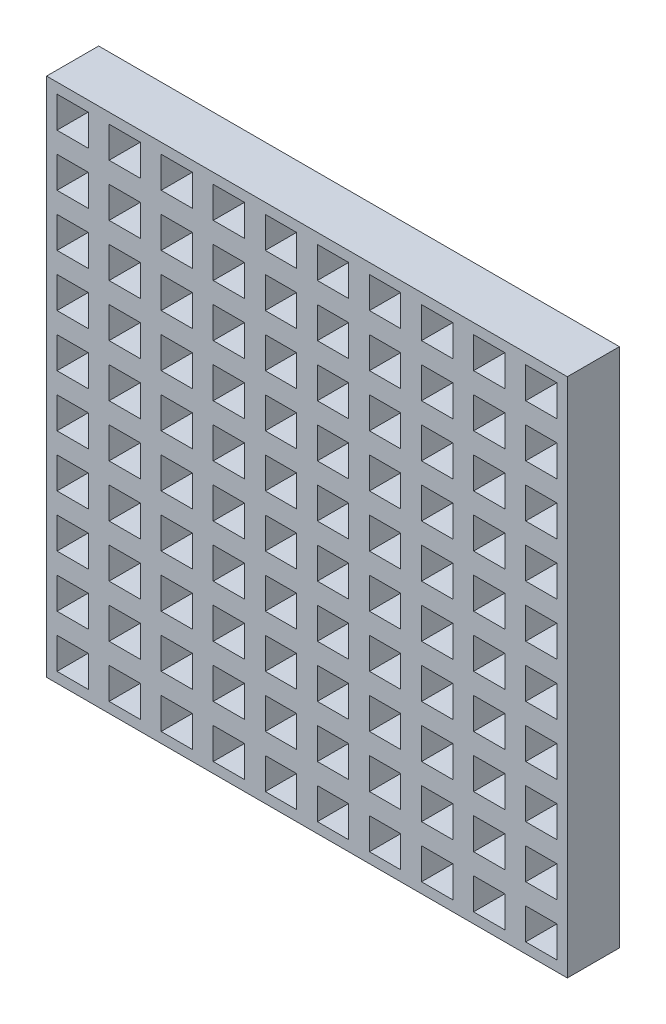
SolidWorks part; units mm, degrees
material "201.0-T7 Insulated Mold Casting (SS)"
ref_plane "Front Plane" through (0, 0, 0) normal (0, 0, 1) x (1, 0, 0)
ref_plane "Top Plane" through (0, 0, 0) normal (0, 1, 0) x (1, 0, 0)
ref_plane "Right Plane" through (0, 0, 0) normal (1, 0, 0) x (0, 0, -1)
sketch "Sketch1" plane through (0, 0, 0) normal (0, 0, 1) x (1, 0, 0)
  line L1 (-12.7, -12.7) -> (12.7, -12.7)
  line L2 (-12.7, -12.7) -> (-12.7, 12.7)
  line L3 (-12.7, 12.7) -> (12.7, 12.7)
  line L4 (12.7, -12.7) -> (12.7, 12.7)
  line L5 (-12.7, -12.7) -> (12.7, 12.7) construction
  line L6 (-12.7, 12.7) -> (12.7, -12.7) construction
  point P0 (0, 0)
  dimension "D1" = 25.4
  dimension "D2" = 25.4
extrude "Boss-Extrude1" add sketch "Sketch1" along normal blind 2.54
sketch "Sketch2" plane through (0, 0, 2.54) normal (0, 0, 1) x (1, 0, 0)
  line L0 (-12.7, 12.7) -> (-12.7, -12.7)
  line L1 (-10.16, 12.7) -> (-10.16, -12.7)
  line L2 (-7.62, 12.7) -> (-7.62, -12.7)
  line L3 (-5.08, 12.7) -> (-5.08, -12.7)
  line L4 (-2.54, 12.7) -> (-2.54, -12.7)
  line L5 (0, 12.7) -> (0, -12.7)
  line L6 (2.54, 12.7) -> (2.54, -12.7)
  line L7 (5.08, 12.7) -> (5.08, -12.7)
  line L8 (7.62, 12.7) -> (7.62, -12.7)
  line L9 (10.16, 12.7) -> (10.16, -12.7)
  line L10 (-12.7, 12.7) -> (12.7, 12.7)
  line L11 (-12.7, 10.16) -> (12.7, 10.16)
  line L12 (12.7, -12.7) -> (12.7, 12.7) construction
  line L13 (-12.7, 7.62) -> (12.7, 7.62)
  line L14 (-12.7, 5.08) -> (12.7, 5.08)
  line L15 (-12.7, 2.54) -> (12.7, 2.54)
  line L16 (-12.7, 0) -> (12.7, 0)
  line L17 (-12.7, -2.54) -> (12.7, -2.54)
  line L18 (-12.7, -5.08) -> (12.7, -5.08)
  line L19 (-12.7, -7.62) -> (12.7, -7.62)
  line L20 (-12.7, -10.16) -> (12.7, -10.16)
  line L21 (-12.192, 12.192) -> (-12.192, 10.668)
  line L22 (-12.7, 12.7) -> (-10.16, 12.7)
  line L23 (-12.7, 12.7) -> (-12.7, 10.16)
  line L24 (-12.7, 10.16) -> (-10.16, 10.16)
  line L25 (-10.16, 12.7) -> (-10.16, 10.16)
  line L26 (-12.192, 10.668) -> (-10.668, 10.668)
  line L27 (-10.668, 12.192) -> (-10.668, 10.668)
  line L28 (-12.192, 12.192) -> (-10.668, 12.192)
  line L29 (-8.128, 12.192) -> (-8.128, 10.668)
  line L30 (-9.652, 12.192) -> (-9.652, 10.668)
  line L31 (-9.652, 12.192) -> (-8.128, 12.192)
  line L32 (-9.652, 10.668) -> (-8.128, 10.668)
  line L33 (-5.588, 12.192) -> (-5.588, 10.668)
  line L34 (-7.112, 12.192) -> (-7.112, 10.668)
  line L35 (-7.112, 12.192) -> (-5.588, 12.192)
  line L36 (-7.112, 10.668) -> (-5.588, 10.668)
  line L37 (-3.048, 12.192) -> (-3.048, 10.668)
  line L38 (-4.572, 12.192) -> (-4.572, 10.668)
  line L39 (-4.572, 12.192) -> (-3.048, 12.192)
  line L40 (-4.572, 10.668) -> (-3.048, 10.668)
  line L41 (-0.508, 12.192) -> (-0.508, 10.668)
  line L42 (-2.032, 12.192) -> (-2.032, 10.668)
  line L43 (-2.032, 12.192) -> (-0.508, 12.192)
  line L44 (-2.032, 10.668) -> (-0.508, 10.668)
  line L45 (2.032, 12.192) -> (2.032, 10.668)
  line L46 (0.508, 12.192) -> (0.508, 10.668)
  line L47 (0.508, 12.192) -> (2.032, 12.192)
  line L48 (0.508, 10.668) -> (2.032, 10.668)
  line L49 (4.572, 12.192) -> (4.572, 10.668)
  line L50 (3.048, 12.192) -> (3.048, 10.668)
  line L51 (3.048, 12.192) -> (4.572, 12.192)
  line L52 (3.048, 10.668) -> (4.572, 10.668)
  line L53 (7.112, 12.192) -> (7.112, 10.668)
  line L54 (5.588, 12.192) -> (5.588, 10.668)
  line L55 (5.588, 12.192) -> (7.112, 12.192)
  line L56 (5.588, 10.668) -> (7.112, 10.668)
  line L57 (9.652, 12.192) -> (9.652, 10.668)
  line L58 (8.128, 12.192) -> (8.128, 10.668)
  line L59 (8.128, 12.192) -> (9.652, 12.192)
  line L60 (8.128, 10.668) -> (9.652, 10.668)
  line L61 (12.192, 12.192) -> (12.192, 10.668)
  line L62 (10.668, 12.192) -> (10.668, 10.668)
  line L63 (10.668, 12.192) -> (12.192, 12.192)
  line L64 (10.668, 10.668) -> (12.192, 10.668)
  line L65 (-8.128, 9.652) -> (-8.128, 8.128)
  line L66 (-9.652, 9.652) -> (-9.652, 8.128)
  line L67 (-9.652, 9.652) -> (-8.128, 9.652)
  line L68 (-9.652, 8.128) -> (-8.128, 8.128)
  line L69 (-5.588, 9.652) -> (-5.588, 8.128)
  line L70 (-7.112, 9.652) -> (-7.112, 8.128)
  line L71 (-7.112, 9.652) -> (-5.588, 9.652)
  line L72 (-7.112, 8.128) -> (-5.588, 8.128)
  line L73 (-3.048, 9.652) -> (-3.048, 8.128)
  line L74 (-4.572, 9.652) -> (-4.572, 8.128)
  line L75 (-4.572, 9.652) -> (-3.048, 9.652)
  line L76 (-4.572, 8.128) -> (-3.048, 8.128)
  line L77 (-0.508, 9.652) -> (-0.508, 8.128)
  line L78 (-2.032, 9.652) -> (-2.032, 8.128)
  line L79 (-2.032, 9.652) -> (-0.508, 9.652)
  line L80 (-2.032, 8.128) -> (-0.508, 8.128)
  line L81 (2.032, 9.652) -> (2.032, 8.128)
  line L82 (0.508, 9.652) -> (0.508, 8.128)
  line L83 (0.508, 9.652) -> (2.032, 9.652)
  line L84 (0.508, 8.128) -> (2.032, 8.128)
  line L85 (4.572, 9.652) -> (4.572, 8.128)
  line L86 (3.048, 9.652) -> (3.048, 8.128)
  line L87 (3.048, 9.652) -> (4.572, 9.652)
  line L88 (3.048, 8.128) -> (4.572, 8.128)
  line L89 (7.112, 9.652) -> (7.112, 8.128)
  line L90 (5.588, 9.652) -> (5.588, 8.128)
  line L91 (5.588, 9.652) -> (7.112, 9.652)
  line L92 (5.588, 8.128) -> (7.112, 8.128)
  line L93 (9.652, 9.652) -> (9.652, 8.128)
  line L94 (8.128, 9.652) -> (8.128, 8.128)
  line L95 (8.128, 9.652) -> (9.652, 9.652)
  line L96 (8.128, 8.128) -> (9.652, 8.128)
  line L97 (12.192, 9.652) -> (12.192, 8.128)
  line L98 (10.668, 9.652) -> (10.668, 8.128)
  line L99 (10.668, 9.652) -> (12.192, 9.652)
  line L100 (10.668, 8.128) -> (12.192, 8.128)
  line L101 (-8.128, 7.112) -> (-8.128, 5.588)
  line L102 (-9.652, 7.112) -> (-9.652, 5.588)
  line L103 (-9.652, 7.112) -> (-8.128, 7.112)
  line L104 (-9.652, 5.588) -> (-8.128, 5.588)
  line L105 (-5.588, 7.112) -> (-5.588, 5.588)
  line L106 (-7.112, 7.112) -> (-7.112, 5.588)
  line L107 (-7.112, 7.112) -> (-5.588, 7.112)
  line L108 (-7.112, 5.588) -> (-5.588, 5.588)
  line L109 (-3.048, 7.112) -> (-3.048, 5.588)
  line L110 (-4.572, 7.112) -> (-4.572, 5.588)
  line L111 (-4.572, 7.112) -> (-3.048, 7.112)
  line L112 (-4.572, 5.588) -> (-3.048, 5.588)
  line L113 (-0.508, 7.112) -> (-0.508, 5.588)
  line L114 (-2.032, 7.112) -> (-2.032, 5.588)
  line L115 (-2.032, 7.112) -> (-0.508, 7.112)
  line L116 (-2.032, 5.588) -> (-0.508, 5.588)
  line L117 (2.032, 7.112) -> (2.032, 5.588)
  line L118 (0.508, 7.112) -> (0.508, 5.588)
  line L119 (0.508, 7.112) -> (2.032, 7.112)
  line L120 (0.508, 5.588) -> (2.032, 5.588)
  line L121 (4.572, 7.112) -> (4.572, 5.588)
  line L122 (3.048, 7.112) -> (3.048, 5.588)
  line L123 (3.048, 7.112) -> (4.572, 7.112)
  line L124 (3.048, 5.588) -> (4.572, 5.588)
  line L125 (7.112, 7.112) -> (7.112, 5.588)
  line L126 (5.588, 7.112) -> (5.588, 5.588)
  line L127 (5.588, 7.112) -> (7.112, 7.112)
  line L128 (5.588, 5.588) -> (7.112, 5.588)
  line L129 (9.652, 7.112) -> (9.652, 5.588)
  line L130 (8.128, 7.112) -> (8.128, 5.588)
  line L131 (8.128, 7.112) -> (9.652, 7.112)
  line L132 (8.128, 5.588) -> (9.652, 5.588)
  line L133 (12.192, 7.112) -> (12.192, 5.588)
  line L134 (10.668, 7.112) -> (10.668, 5.588)
  line L135 (10.668, 7.112) -> (12.192, 7.112)
  line L136 (10.668, 5.588) -> (12.192, 5.588)
  line L137 (-8.128, 4.572) -> (-8.128, 3.048)
  line L138 (-9.652, 4.572) -> (-9.652, 3.048)
  line L139 (-9.652, 4.572) -> (-8.128, 4.572)
  line L140 (-9.652, 3.048) -> (-8.128, 3.048)
  line L141 (-5.588, 4.572) -> (-5.588, 3.048)
  line L142 (-7.112, 4.572) -> (-7.112, 3.048)
  line L143 (-7.112, 4.572) -> (-5.588, 4.572)
  line L144 (-7.112, 3.048) -> (-5.588, 3.048)
  line L145 (-3.048, 4.572) -> (-3.048, 3.048)
  line L146 (-4.572, 4.572) -> (-4.572, 3.048)
  line L147 (-4.572, 4.572) -> (-3.048, 4.572)
  line L148 (-4.572, 3.048) -> (-3.048, 3.048)
  line L149 (-0.508, 4.572) -> (-0.508, 3.048)
  line L150 (-2.032, 4.572) -> (-2.032, 3.048)
  line L151 (-2.032, 4.572) -> (-0.508, 4.572)
  line L152 (-2.032, 3.048) -> (-0.508, 3.048)
  line L153 (2.032, 4.572) -> (2.032, 3.048)
  line L154 (0.508, 4.572) -> (0.508, 3.048)
  line L155 (0.508, 4.572) -> (2.032, 4.572)
  line L156 (0.508, 3.048) -> (2.032, 3.048)
  line L157 (4.572, 4.572) -> (4.572, 3.048)
  line L158 (3.048, 4.572) -> (3.048, 3.048)
  line L159 (3.048, 4.572) -> (4.572, 4.572)
  line L160 (3.048, 3.048) -> (4.572, 3.048)
  line L161 (7.112, 4.572) -> (7.112, 3.048)
  line L162 (5.588, 4.572) -> (5.588, 3.048)
  line L163 (5.588, 4.572) -> (7.112, 4.572)
  line L164 (5.588, 3.048) -> (7.112, 3.048)
  line L165 (9.652, 4.572) -> (9.652, 3.048)
  line L166 (8.128, 4.572) -> (8.128, 3.048)
  line L167 (8.128, 4.572) -> (9.652, 4.572)
  line L168 (8.128, 3.048) -> (9.652, 3.048)
  line L169 (12.192, 4.572) -> (12.192, 3.048)
  line L170 (10.668, 4.572) -> (10.668, 3.048)
  line L171 (10.668, 4.572) -> (12.192, 4.572)
  line L172 (10.668, 3.048) -> (12.192, 3.048)
  line L173 (-8.128, 2.032) -> (-8.128, 0.508)
  line L174 (-9.652, 2.032) -> (-9.652, 0.508)
  line L175 (-9.652, 2.032) -> (-8.128, 2.032)
  line L176 (-9.652, 0.508) -> (-8.128, 0.508)
  line L177 (-5.588, 2.032) -> (-5.588, 0.508)
  line L178 (-7.112, 2.032) -> (-7.112, 0.508)
  line L179 (-7.112, 2.032) -> (-5.588, 2.032)
  line L180 (-7.112, 0.508) -> (-5.588, 0.508)
  line L181 (-3.048, 2.032) -> (-3.048, 0.508)
  line L182 (-4.572, 2.032) -> (-4.572, 0.508)
  line L183 (-4.572, 2.032) -> (-3.048, 2.032)
  line L184 (-4.572, 0.508) -> (-3.048, 0.508)
  line L185 (-0.508, 2.032) -> (-0.508, 0.508)
  line L186 (-2.032, 2.032) -> (-2.032, 0.508)
  line L187 (-2.032, 2.032) -> (-0.508, 2.032)
  line L188 (-2.032, 0.508) -> (-0.508, 0.508)
  line L189 (2.032, 2.032) -> (2.032, 0.508)
  line L190 (0.508, 2.032) -> (0.508, 0.508)
  line L191 (0.508, 2.032) -> (2.032, 2.032)
  line L192 (0.508, 0.508) -> (2.032, 0.508)
  line L193 (4.572, 2.032) -> (4.572, 0.508)
  line L194 (3.048, 2.032) -> (3.048, 0.508)
  line L195 (3.048, 2.032) -> (4.572, 2.032)
  line L196 (3.048, 0.508) -> (4.572, 0.508)
  line L197 (7.112, 2.032) -> (7.112, 0.508)
  line L198 (5.588, 2.032) -> (5.588, 0.508)
  line L199 (5.588, 2.032) -> (7.112, 2.032)
  line L200 (5.588, 0.508) -> (7.112, 0.508)
  line L201 (9.652, 2.032) -> (9.652, 0.508)
  line L202 (8.128, 2.032) -> (8.128, 0.508)
  line L203 (8.128, 2.032) -> (9.652, 2.032)
  line L204 (8.128, 0.508) -> (9.652, 0.508)
  line L205 (12.192, 2.032) -> (12.192, 0.508)
  line L206 (10.668, 2.032) -> (10.668, 0.508)
  line L207 (10.668, 2.032) -> (12.192, 2.032)
  line L208 (10.668, 0.508) -> (12.192, 0.508)
  line L209 (-8.128, -0.508) -> (-8.128, -2.032)
  line L210 (-9.652, -0.508) -> (-9.652, -2.032)
  line L211 (-9.652, -0.508) -> (-8.128, -0.508)
  line L212 (-9.652, -2.032) -> (-8.128, -2.032)
  line L213 (-5.588, -0.508) -> (-5.588, -2.032)
  line L214 (-7.112, -0.508) -> (-7.112, -2.032)
  line L215 (-7.112, -0.508) -> (-5.588, -0.508)
  line L216 (-7.112, -2.032) -> (-5.588, -2.032)
  line L217 (-3.048, -0.508) -> (-3.048, -2.032)
  line L218 (-4.572, -0.508) -> (-4.572, -2.032)
  line L219 (-4.572, -0.508) -> (-3.048, -0.508)
  line L220 (-4.572, -2.032) -> (-3.048, -2.032)
  line L221 (-0.508, -0.508) -> (-0.508, -2.032)
  line L222 (-2.032, -0.508) -> (-2.032, -2.032)
  line L223 (-2.032, -0.508) -> (-0.508, -0.508)
  line L224 (-2.032, -2.032) -> (-0.508, -2.032)
  line L225 (2.032, -0.508) -> (2.032, -2.032)
  line L226 (0.508, -0.508) -> (0.508, -2.032)
  line L227 (0.508, -0.508) -> (2.032, -0.508)
  line L228 (0.508, -2.032) -> (2.032, -2.032)
  line L229 (4.572, -0.508) -> (4.572, -2.032)
  line L230 (3.048, -0.508) -> (3.048, -2.032)
  line L231 (3.048, -0.508) -> (4.572, -0.508)
  line L232 (3.048, -2.032) -> (4.572, -2.032)
  line L233 (7.112, -0.508) -> (7.112, -2.032)
  line L234 (5.588, -0.508) -> (5.588, -2.032)
  line L235 (5.588, -0.508) -> (7.112, -0.508)
  line L236 (5.588, -2.032) -> (7.112, -2.032)
  line L237 (9.652, -0.508) -> (9.652, -2.032)
  line L238 (8.128, -0.508) -> (8.128, -2.032)
  line L239 (8.128, -0.508) -> (9.652, -0.508)
  line L240 (8.128, -2.032) -> (9.652, -2.032)
  line L241 (12.192, -0.508) -> (12.192, -2.032)
  line L242 (10.668, -0.508) -> (10.668, -2.032)
  line L243 (10.668, -0.508) -> (12.192, -0.508)
  line L244 (10.668, -2.032) -> (12.192, -2.032)
  line L245 (-8.128, -3.048) -> (-8.128, -4.572)
  line L246 (-9.652, -3.048) -> (-9.652, -4.572)
  line L247 (-9.652, -3.048) -> (-8.128, -3.048)
  line L248 (-9.652, -4.572) -> (-8.128, -4.572)
  line L249 (-5.588, -3.048) -> (-5.588, -4.572)
  line L250 (-7.112, -3.048) -> (-7.112, -4.572)
  line L251 (-7.112, -3.048) -> (-5.588, -3.048)
  line L252 (-7.112, -4.572) -> (-5.588, -4.572)
  line L253 (-3.048, -3.048) -> (-3.048, -4.572)
  line L254 (-4.572, -3.048) -> (-4.572, -4.572)
  line L255 (-4.572, -3.048) -> (-3.048, -3.048)
  line L256 (-4.572, -4.572) -> (-3.048, -4.572)
  line L257 (-0.508, -3.048) -> (-0.508, -4.572)
  line L258 (-2.032, -3.048) -> (-2.032, -4.572)
  line L259 (-2.032, -3.048) -> (-0.508, -3.048)
  line L260 (-2.032, -4.572) -> (-0.508, -4.572)
  line L261 (2.032, -3.048) -> (2.032, -4.572)
  line L262 (0.508, -3.048) -> (0.508, -4.572)
  line L263 (0.508, -3.048) -> (2.032, -3.048)
  line L264 (0.508, -4.572) -> (2.032, -4.572)
  line L265 (4.572, -3.048) -> (4.572, -4.572)
  line L266 (3.048, -3.048) -> (3.048, -4.572)
  line L267 (3.048, -3.048) -> (4.572, -3.048)
  line L268 (3.048, -4.572) -> (4.572, -4.572)
  line L269 (7.112, -3.048) -> (7.112, -4.572)
  line L270 (5.588, -3.048) -> (5.588, -4.572)
  line L271 (5.588, -3.048) -> (7.112, -3.048)
  line L272 (5.588, -4.572) -> (7.112, -4.572)
  line L273 (9.652, -3.048) -> (9.652, -4.572)
  line L274 (8.128, -3.048) -> (8.128, -4.572)
  line L275 (8.128, -3.048) -> (9.652, -3.048)
  line L276 (8.128, -4.572) -> (9.652, -4.572)
  line L277 (12.192, -3.048) -> (12.192, -4.572)
  line L278 (10.668, -3.048) -> (10.668, -4.572)
  line L279 (10.668, -3.048) -> (12.192, -3.048)
  line L280 (10.668, -4.572) -> (12.192, -4.572)
  line L281 (-8.128, -5.588) -> (-8.128, -7.112)
  line L282 (-9.652, -5.588) -> (-9.652, -7.112)
  line L283 (-9.652, -5.588) -> (-8.128, -5.588)
  line L284 (-9.652, -7.112) -> (-8.128, -7.112)
  line L285 (-5.588, -5.588) -> (-5.588, -7.112)
  line L286 (-7.112, -5.588) -> (-7.112, -7.112)
  line L287 (-7.112, -5.588) -> (-5.588, -5.588)
  line L288 (-7.112, -7.112) -> (-5.588, -7.112)
  line L289 (-3.048, -5.588) -> (-3.048, -7.112)
  line L290 (-4.572, -5.588) -> (-4.572, -7.112)
  line L291 (-4.572, -5.588) -> (-3.048, -5.588)
  line L292 (-4.572, -7.112) -> (-3.048, -7.112)
  line L293 (-0.508, -5.588) -> (-0.508, -7.112)
  line L294 (-2.032, -5.588) -> (-2.032, -7.112)
  line L295 (-2.032, -5.588) -> (-0.508, -5.588)
  line L296 (-2.032, -7.112) -> (-0.508, -7.112)
  line L297 (2.032, -5.588) -> (2.032, -7.112)
  line L298 (0.508, -5.588) -> (0.508, -7.112)
  line L299 (0.508, -5.588) -> (2.032, -5.588)
  line L300 (0.508, -7.112) -> (2.032, -7.112)
  line L301 (4.572, -5.588) -> (4.572, -7.112)
  line L302 (3.048, -5.588) -> (3.048, -7.112)
  line L303 (3.048, -5.588) -> (4.572, -5.588)
  line L304 (3.048, -7.112) -> (4.572, -7.112)
  line L305 (7.112, -5.588) -> (7.112, -7.112)
  line L306 (5.588, -5.588) -> (5.588, -7.112)
  line L307 (5.588, -5.588) -> (7.112, -5.588)
  line L308 (5.588, -7.112) -> (7.112, -7.112)
  line L309 (9.652, -5.588) -> (9.652, -7.112)
  line L310 (8.128, -5.588) -> (8.128, -7.112)
  line L311 (8.128, -5.588) -> (9.652, -5.588)
  line L312 (8.128, -7.112) -> (9.652, -7.112)
  line L313 (12.192, -5.588) -> (12.192, -7.112)
  line L314 (10.668, -5.588) -> (10.668, -7.112)
  line L315 (10.668, -5.588) -> (12.192, -5.588)
  line L316 (10.668, -7.112) -> (12.192, -7.112)
  line L317 (-8.128, -8.128) -> (-8.128, -9.652)
  line L318 (-9.652, -8.128) -> (-9.652, -9.652)
  line L319 (-9.652, -8.128) -> (-8.128, -8.128)
  line L320 (-9.652, -9.652) -> (-8.128, -9.652)
  line L321 (-5.588, -8.128) -> (-5.588, -9.652)
  line L322 (-7.112, -8.128) -> (-7.112, -9.652)
  line L323 (-7.112, -8.128) -> (-5.588, -8.128)
  line L324 (-7.112, -9.652) -> (-5.588, -9.652)
  line L325 (-3.048, -8.128) -> (-3.048, -9.652)
  line L326 (-4.572, -8.128) -> (-4.572, -9.652)
  line L327 (-4.572, -8.128) -> (-3.048, -8.128)
  line L328 (-4.572, -9.652) -> (-3.048, -9.652)
  line L329 (-0.508, -8.128) -> (-0.508, -9.652)
  line L330 (-2.032, -8.128) -> (-2.032, -9.652)
  line L331 (-2.032, -8.128) -> (-0.508, -8.128)
  line L332 (-2.032, -9.652) -> (-0.508, -9.652)
  line L333 (2.032, -8.128) -> (2.032, -9.652)
  line L334 (0.508, -8.128) -> (0.508, -9.652)
  line L335 (0.508, -8.128) -> (2.032, -8.128)
  line L336 (0.508, -9.652) -> (2.032, -9.652)
  line L337 (4.572, -8.128) -> (4.572, -9.652)
  line L338 (3.048, -8.128) -> (3.048, -9.652)
  line L339 (3.048, -8.128) -> (4.572, -8.128)
  line L340 (3.048, -9.652) -> (4.572, -9.652)
  line L341 (7.112, -8.128) -> (7.112, -9.652)
  line L342 (5.588, -8.128) -> (5.588, -9.652)
  line L343 (5.588, -8.128) -> (7.112, -8.128)
  line L344 (5.588, -9.652) -> (7.112, -9.652)
  line L345 (9.652, -8.128) -> (9.652, -9.652)
  line L346 (8.128, -8.128) -> (8.128, -9.652)
  line L347 (8.128, -8.128) -> (9.652, -8.128)
  line L348 (8.128, -9.652) -> (9.652, -9.652)
  line L349 (12.192, -8.128) -> (12.192, -9.652)
  line L350 (10.668, -8.128) -> (10.668, -9.652)
  line L351 (10.668, -8.128) -> (12.192, -8.128)
  line L352 (10.668, -9.652) -> (12.192, -9.652)
  line L353 (-8.128, -10.668) -> (-8.128, -12.192)
  line L354 (-9.652, -10.668) -> (-9.652, -12.192)
  line L355 (-9.652, -10.668) -> (-8.128, -10.668)
  line L356 (-9.652, -12.192) -> (-8.128, -12.192)
  line L357 (-5.588, -10.668) -> (-5.588, -12.192)
  line L358 (-7.112, -10.668) -> (-7.112, -12.192)
  line L359 (-7.112, -10.668) -> (-5.588, -10.668)
  line L360 (-7.112, -12.192) -> (-5.588, -12.192)
  line L361 (-3.048, -10.668) -> (-3.048, -12.192)
  line L362 (-4.572, -10.668) -> (-4.572, -12.192)
  line L363 (-4.572, -10.668) -> (-3.048, -10.668)
  line L364 (-4.572, -12.192) -> (-3.048, -12.192)
  line L365 (-0.508, -10.668) -> (-0.508, -12.192)
  line L366 (-2.032, -10.668) -> (-2.032, -12.192)
  line L367 (-2.032, -10.668) -> (-0.508, -10.668)
  line L368 (-2.032, -12.192) -> (-0.508, -12.192)
  line L369 (2.032, -10.668) -> (2.032, -12.192)
  line L370 (0.508, -10.668) -> (0.508, -12.192)
  line L371 (0.508, -10.668) -> (2.032, -10.668)
  line L372 (0.508, -12.192) -> (2.032, -12.192)
  line L373 (4.572, -10.668) -> (4.572, -12.192)
  line L374 (3.048, -10.668) -> (3.048, -12.192)
  line L375 (3.048, -10.668) -> (4.572, -10.668)
  line L376 (3.048, -12.192) -> (4.572, -12.192)
  line L377 (7.112, -10.668) -> (7.112, -12.192)
  line L378 (5.588, -10.668) -> (5.588, -12.192)
  line L379 (5.588, -10.668) -> (7.112, -10.668)
  line L380 (5.588, -12.192) -> (7.112, -12.192)
  line L381 (9.652, -10.668) -> (9.652, -12.192)
  line L382 (8.128, -10.668) -> (8.128, -12.192)
  line L383 (8.128, -10.668) -> (9.652, -10.668)
  line L384 (8.128, -12.192) -> (9.652, -12.192)
  line L385 (12.192, -10.668) -> (12.192, -12.192)
  line L386 (10.668, -10.668) -> (10.668, -12.192)
  line L387 (10.668, -10.668) -> (12.192, -10.668)
  line L388 (10.668, -12.192) -> (12.192, -12.192)
  line L389 (-10.668, 9.652) -> (-10.668, 8.128)
  line L390 (-12.192, 9.652) -> (-12.192, 8.128)
  line L391 (-12.192, 9.652) -> (-10.668, 9.652)
  line L392 (-12.192, 8.128) -> (-10.668, 8.128)
  line L393 (-10.668, 7.112) -> (-10.668, 5.588)
  line L394 (-12.192, 7.112) -> (-12.192, 5.588)
  line L395 (-12.192, 7.112) -> (-10.668, 7.112)
  line L396 (-12.192, 5.588) -> (-10.668, 5.588)
  line L397 (-10.668, 4.572) -> (-10.668, 3.048)
  line L398 (-12.192, 4.572) -> (-12.192, 3.048)
  line L399 (-12.192, 4.572) -> (-10.668, 4.572)
  line L400 (-12.192, 3.048) -> (-10.668, 3.048)
  line L401 (-10.668, 2.032) -> (-10.668, 0.508)
  line L402 (-12.192, 2.032) -> (-12.192, 0.508)
  line L403 (-12.192, 2.032) -> (-10.668, 2.032)
  line L404 (-12.192, 0.508) -> (-10.668, 0.508)
  line L405 (-10.668, -0.508) -> (-10.668, -2.032)
  line L406 (-12.192, -0.508) -> (-12.192, -2.032)
  line L407 (-12.192, -0.508) -> (-10.668, -0.508)
  line L408 (-12.192, -2.032) -> (-10.668, -2.032)
  line L409 (-10.668, -3.048) -> (-10.668, -4.572)
  line L410 (-12.192, -3.048) -> (-12.192, -4.572)
  line L411 (-12.192, -3.048) -> (-10.668, -3.048)
  line L412 (-12.192, -4.572) -> (-10.668, -4.572)
  line L413 (-10.668, -5.588) -> (-10.668, -7.112)
  line L414 (-12.192, -5.588) -> (-12.192, -7.112)
  line L415 (-12.192, -5.588) -> (-10.668, -5.588)
  line L416 (-12.192, -7.112) -> (-10.668, -7.112)
  line L417 (-10.668, -8.128) -> (-10.668, -9.652)
  line L418 (-12.192, -8.128) -> (-12.192, -9.652)
  line L419 (-12.192, -8.128) -> (-10.668, -8.128)
  line L420 (-12.192, -9.652) -> (-10.668, -9.652)
  line L421 (-10.668, -10.668) -> (-10.668, -12.192)
  line L422 (-12.192, -10.668) -> (-12.192, -12.192)
  line L423 (-12.192, -10.668) -> (-10.668, -10.668)
  line L424 (-12.192, -12.192) -> (-10.668, -12.192)
  dimension "D1" = 2.54
  dimension "D10" = 2.54
  dimension "D19" = 0.508
  dimension "D20" = 10
  dimension "D2" = 2.54
  dimension "D3" = 2.54
  dimension "D4" = 2.54
  dimension "D5" = 2.54
  dimension "D6" = 2.54
  dimension "D7" = 2.54
  dimension "D8" = 2.54
  dimension "D9" = 2.54
  dimension "D11" = 2.54
  dimension "D12" = 2.54
  dimension "D13" = 2.54
  dimension "D14" = 2.54
  dimension "D15" = 2.54
  dimension "D16" = 2.54
  dimension "D17" = 2.54
  dimension "D18" = 2.54
  dimension "D21" = 10
extrude "Cut-Extrude1" cut sketch "Sketch2" against normal blind 2.54 contours L390 L392 L389 L391 | L398 L400 L397 L399 | L406 L408 L405 L407 | L410 L412 L409 L411 | L414 L416 L413 L415 | L418 L420 L417 L419 | L422 L424 L421 L423 | L354 L356 L353 L355 | L318 L320 L317 L319 | L282 L284 L281 L283 | L246 L248 L245 L247 | L210 L212 L209 L211 | L174 L176 L173 L175 | L102 L104 L101 L103 | L66 L68 L65 L67 | L30 L32 L29 L31 | L28 L21 L26 L27 | L402 L404 L401 L403 | L138 L140 L137 L139 | L394 L396 L393 L395
pattern_linear "LPattern1" count 9 spacing 2.54 along (1, 0, 0) of "Cut-Extrude1"
